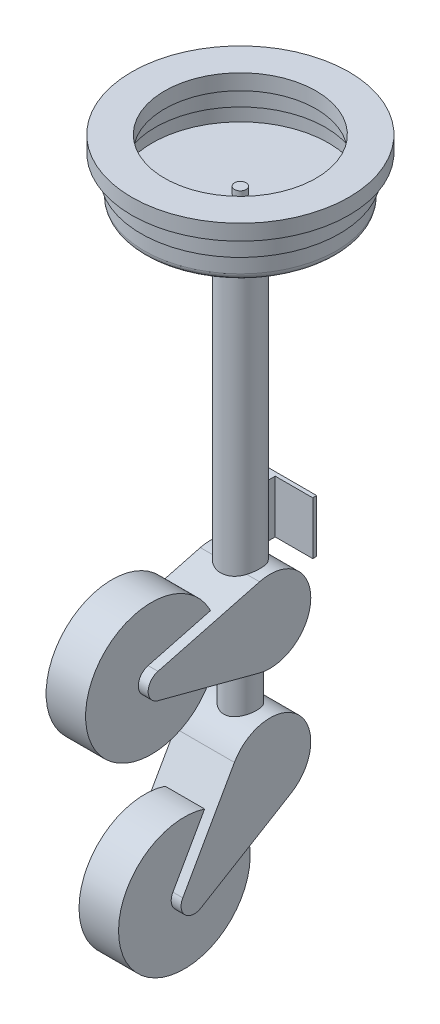
SolidWorks part; units mm, degrees
ref_plane "Front Plane" through (0, 0, 0) normal (0, 0, 1) x (1, 0, 0)
ref_plane "Top Plane" through (0, 0, 0) normal (0, 1, 0) x (1, 0, 0)
ref_plane "Right Plane" through (0, 0, 0) normal (1, 0, 0) x (0, 0, -1)
sketch "Sketch1" plane through (0, 0, 0) normal (0, 0, 1) x (1, 0, 0)
  line L1 (-70, -40) -> (70, -40)
  line L2 (-70, -40) -> (-70, 40)
  line L3 (-70, 40) -> (70, 40)
  line L4 (70, -40) -> (70, 40)
  line L5 (-70, -40) -> (70, 40) construction
  line L6 (-70, 40) -> (70, -40) construction
  point P0 (0, 0)
  dimension "D1" = 140
  dimension "D2" = 80
extrude "Boss-Extrude1" add sketch "Sketch1" along normal blind 6
sketch "Sketch2" plane through (0, 0, 0) normal (0, 1, 0) x (1, 0, 0)
  line L0 (0, -16) -> (-45.1893, -16) construction
  line L1 (70, -6) -> (-70, -6) construction
  circle A0 centre (0, -46) radius 30
  dimension "D1" = 60
  dimension "D2" = 10
extrude "Boss-Extrude2" add sketch "Sketch2" along normal blind 400 and the other way blind 70 separate body
sketch "Sketch3" plane through (0, -70, 0) normal (0, -1, 0) x (1, 0, 0)
  circle A0 centre (0, 46) radius 25
  circle A1 centre (0, 46) radius 30 construction
  dimension "D1" = 50
extrude "Boss-Extrude3" add sketch "Sketch3" along normal blind 45
sketch "Sketch4" plane through (0, 0, 0) normal (1, 0, 0) x (0, 0, -1)
  line L0 (-71, -115) -> (-21, -115) construction
  line L4 (-46, -115) -> (-46, -228.2681) construction
  line L5 (-46, -115) -> (-211, -115) construction
  line L6 (-61.7818, -174.9578) -> (-216.0909, -134.3412)
  line L7 (-61.7818, -55.0422) -> (-216.0909, -95.6588)
  arc A2 (-216.0909, -134.3412) -> (-216.0909, -95.6588) centre (-211, -115) cw
  arc A3 (-61.7818, -55.0422) -> (-61.7818, -174.9578) centre (-46, -115) cw
  dimension "D1" = 20
  dimension "D3" = 165
  dimension "D2" = 62
extrude "Boss-Extrude4" add sketch "Sketch4" along normal blind 45 and the other way blind 45 separate body
sketch "Sketch6" plane through (0, 0, 0) normal (1, 0, 0) x (0, 0, -1)
  circle A0 centre (-211, -115) radius 100
  arc A1 (-216.0909, -95.6588) -> (-216.0909, -134.3412) centre (-211, -115) ccw construction
  dimension "D1" = 200
extrude "Boss-Extrude5" add sketch "Sketch6" along normal blind 30 and the other way blind 30
sketch "Sketch7" plane through (0, 0, 6) normal (0, 0, 1) x (1, 0, 0)
  line L0 (70, 40) -> (-70, 40) construction
  line L1 (-12.9638, -40) -> (12.9638, -40)
  line L2 (-12.9638, -40) -> (-12.9638, 40)
  line L3 (-12.9638, 40) -> (12.9638, 40)
  line L4 (12.9638, -40) -> (12.9638, 40)
  line L5 (-12.9638, -40) -> (12.9638, 40) construction
  line L6 (-12.9638, 40) -> (12.9638, -40) construction
  point P0 (0, 0)
extrude "Boss-Extrude6" add sketch "Sketch7" along normal up to next
sketch "Sketch8" plane through (0, 0, 0) normal (1, 0, 0) x (0, 0, -1)
  line L0 (-46, 400) -> (-46, 466.854) construction
  line L1 (-16, 400) -> (-76, 400) construction
  line L2 (-46, 400) -> (-46, 435)
  line L3 (-46, 435) -> (-54.8233, 435)
  line L4 (-54.8233, 435) -> (-54.8233, 424.8027)
  line L5 (-54.8233, 424.8027) -> (-180, 424.8027)
  line L6 (-180, 424.8027) -> (-180, 447.8027)
  line L7 (-180, 447.8027) -> (-175.1939, 447.8027)
  line L8 (-175.1939, 447.8027) -> (-175.1939, 479.1931)
  line L9 (-175.1939, 479.1931) -> (-161, 479.1931)
  line L10 (-161, 479.1931) -> (-161, 502.8027)
  line L11 (-161, 502.8027) -> (-211, 502.8027)
  line L12 (-211, 502.8027) -> (-211, 479.1931)
  line L13 (-211, 479.1931) -> (-196.8061, 479.1931)
  line L14 (-196.8061, 479.1931) -> (-196.8061, 447.8027)
  line L15 (-196.8061, 447.8027) -> (-192, 447.8027)
  line L16 (-192, 447.8027) -> (-192, 422.8027)
  line L17 (-182, 412.8027) -> (-54.8233, 412.8027)
  line L18 (-54.8233, 412.8027) -> (-54.8233, 400)
  line L19 (-54.8233, 400) -> (-46, 400)
  line L20 (-186, 502.8027) -> (-186, 405.9247) construction
  line L21 (-180, 436.3027) -> (-186, 436.3027) construction
  line L22 (-186, 436.3027) -> (-192, 436.3027) construction
  line L23 (-175.1939, 463.4979) -> (-186, 463.4979) construction
  line L24 (-186, 463.4979) -> (-196.8061, 463.4979) construction
  line L25 (-161, 490.9979) -> (-186, 490.9979) construction
  line L26 (-186, 490.9979) -> (-211, 490.9979) construction
  arc A0 (-192, 422.8027) -> (-182, 412.8027) centre (-182, 422.8027) ccw
  dimension "D1" = 10
  dimension "D2" = 140
  dimension "D3" = 35
  dimension "D4" = 35
  dimension "D5" = 55
  dimension "D6" = 12
  dimension "D7" = 12
  dimension "D8" = 50
revolve "Revolve1" add sketch "Sketch8" angle 360 about L0
sketch "Sketch9" plane through (0, -115, 0) normal (0, -1, 0) x (1, 0, 0)
  circle A0 centre (0, 46) radius 25
extrude "Boss-Extrude7" add sketch "Sketch9" along normal blind 189 separate body
sketch "Sketch10" plane through (0, 0, 0) normal (1, 0, 0) x (0, 0, -1)
  line L0 (-71, -304) -> (-21, -304) construction
  line L1 (-178.4178, -412.492) -> (-99.9952, -273.5284)
  line L2 (-14.0037, -357.1059) -> (-150.6786, -439.4525)
  arc A0 (-14.0037, -357.1059) -> (-99.9952, -273.5284) centre (-46, -304) ccw
  arc A1 (-178.4178, -412.492) -> (-150.6786, -439.4525) centre (-161, -422.3216) ccw
  arc A2 (-61.7818, -174.9578) -> (-61.7818, -55.0422) centre (-46, -115) ccw construction
  arc A3 (-216.0909, -95.6588) -> (-216.0909, -134.3412) centre (-211, -115) ccw construction
  dimension "D1" = 165
  dimension "D2" = 115
extrude "Boss-Extrude8" add sketch "Sketch10" along normal blind 45 and the other way blind 45
sketch "Sketch11" plane through (0, 0, 0) normal (1, 0, 0) x (0, 0, -1)
  circle A0 centre (-161, -422.3216) radius 100
  circle A1 centre (-211, -115) radius 100 construction
extrude "Boss-Extrude9" add sketch "Sketch11" along normal blind 30 and the other way blind 30
sketch3d "3DSketch1"
  line L0 (-45, -422.3216, 161) -> (45, -422.3216, 161) construction
  line L1 (-45, -422.3216, 161) -> (-30, -422.3216, 161) construction
  line L2 (30, -422.3216, 161) -> (45, -422.3216, 161) construction
  line L3 (30, -522.3216, 161) -> (30, -422.3216, 161) construction
  line L4 (-30, -422.3216, 161) -> (-30, -522.3216, 161) construction
  arc A0 (30, -327.1626, 130.2631) -> (30, -388.8883, 66.7545) centre (30, -422.3216, 161) ccw construction
  arc A1 (-30, -327.1626, 130.2631) -> (-30, -388.8883, 66.7545) centre (-30, -422.3216, 161) ccw construction
  point P0 (30, -522.3216, 161)
  point P1 (-30, -522.3216, 161)
  point P5 (130, -422.3216, 161)
  point P10 (70, -422.3216, 161)
